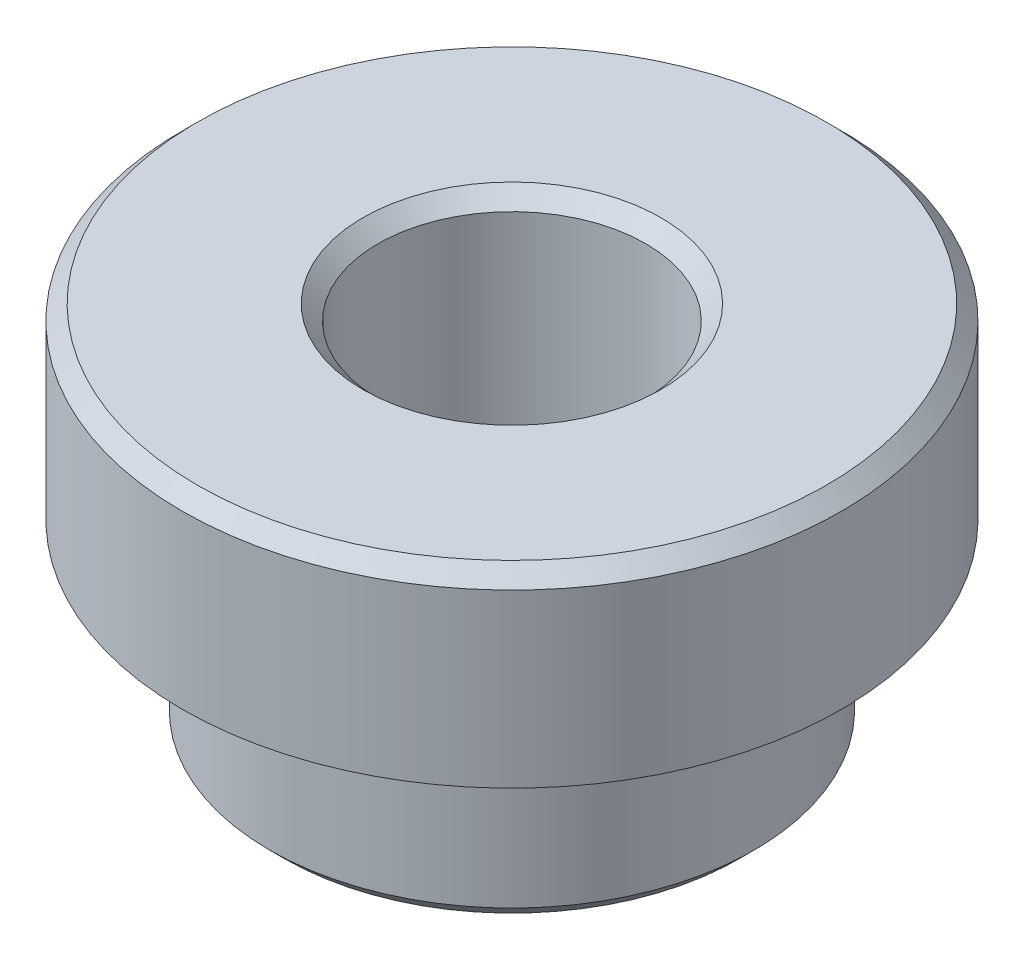
SolidWorks part; units mm, degrees
ref_plane "Front Plane" through (0, 0, 0) normal (0, 0, 1) x (1, 0, 0)
ref_plane "Top Plane" through (0, 0, 0) normal (0, 1, 0) x (1, 0, 0)
ref_plane "Right Plane" through (0, 0, 0) normal (1, 0, 0) x (0, 0, -1)
sketch "Sketch1" plane through (0, 0, 0) normal (0, 1, 0) x (1, 0, 0)
  circle A0 centre (0, 0) radius 2.0447
  dimension "D1" = 4.0894
extrude "Boss-Extrude1" add sketch "Sketch1" along normal blind 1.524
sketch "Sketch2" plane through (0, 1.524, 0) normal (0, 1, 0) x (1, 0, 0)
  circle A0 centre (0, 0) radius 2.7813
  dimension "D1" = 5.5626
extrude "Boss-Extrude2" add sketch "Sketch2" along normal blind 1.5748
hole_wizard "#4-40 Tapped Hole1" positions "Sketch3" profile "Sketch5" tap size "#4-40" standard "ANSI Inch" end condition through all
sketch "Sketch3" plane through (0, 3.0988, 0) normal (0, 1, 0) x (1, 0, 0)
  point P0 (0, 0)
sketch "Sketch5" plane through (0, 3.0988, 0) normal (1, 0, 0) x (0, 0, 1)
  line L0 (0, 0) -> (0, 3.0988)
  line L1 (0, 3.0988) -> (1.1303, 3.0988)
  line L2 (1.1303, 3.0988) -> (1.1303, 0)
  line L5 (1.1303, 0) -> (0, 0)
  line L11 (0, -6.35) -> (0, 107.95) construction
  dimension "Thru Tap Drill Dia." = 2.2606
  dimension "Thru Tap Drill Depth" = 3.0988
cosmetic thread "Hole Thread1" parameters "D2"=2.8448
chamfer "Chamfer1" distance 0.127 angle 45 3 edges at (0, 0, 2.0447) (0, 3.0988, 2.7813) (0, 3.0988, 1.1303)
